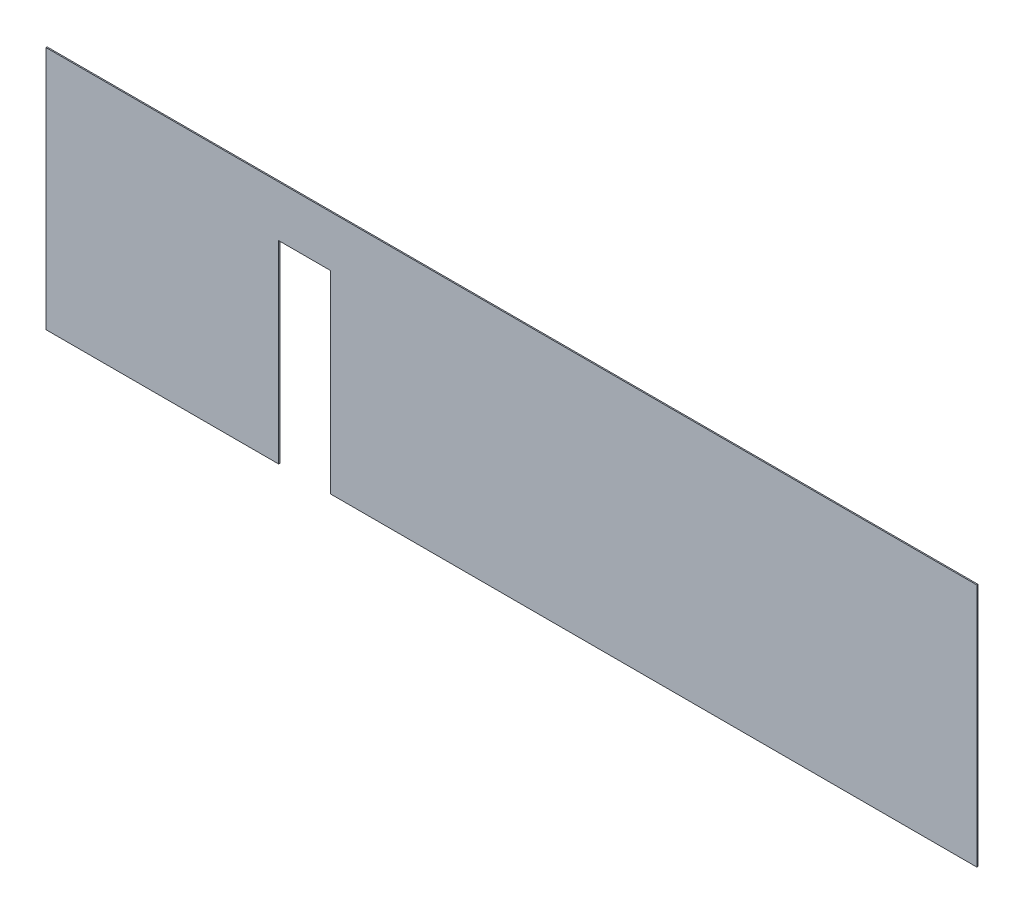
SolidWorks part; units mm, degrees
ref_plane "Front Plane" through (0, 0, 0) normal (0, 0, 1) x (1, 0, 0)
ref_plane "Top Plane" through (0, 0, 0) normal (0, 1, 0) x (1, 0, 0)
ref_plane "Right Plane" through (0, 0, 0) normal (1, 0, 0) x (0, 0, -1)
sketch "Sketch1" plane through (0, 0, 0) normal (0, 0, 1) x (1, 0, 0)
  line L1 (-4000, 1050) -> (4000, 1050)
  line L2 (-4000, 1050) -> (-4000, -1050)
  line L3 (-4000, -1050) -> (4000, -1050)
  line L4 (4000, 1050) -> (4000, -1050)
  line L5 (-4000, 1050) -> (4000, -1050) construction
  line L6 (-4000, -1050) -> (4000, 1050) construction
  point P0 (0, 0)
  dimension "D1" = 2100
  dimension "D2" = 8000
extrude "Boss-Extrude1" add sketch "Sketch1" along normal blind 10
sketch "Sketch2" plane through (0, 0, 10) normal (0, 0, 1) x (1, 0, 0)
  line L0 (-4000, -1050) -> (4000, -1050) construction
  line L1 (-2000, -1050) -> (-1553, -1050)
  line L2 (-2000, -1050) -> (-2000, 613)
  line L3 (-2000, 613) -> (-1553, 613)
  line L4 (-1553, -1050) -> (-1553, 613)
  line L5 (-4000, 1050) -> (-4000, -1050) construction
  dimension "D1" = 2000
  dimension "D2" = 447
  dimension "D3" = 1663
extrude "Cut-Extrude1" cut sketch "Sketch2" against normal through all
